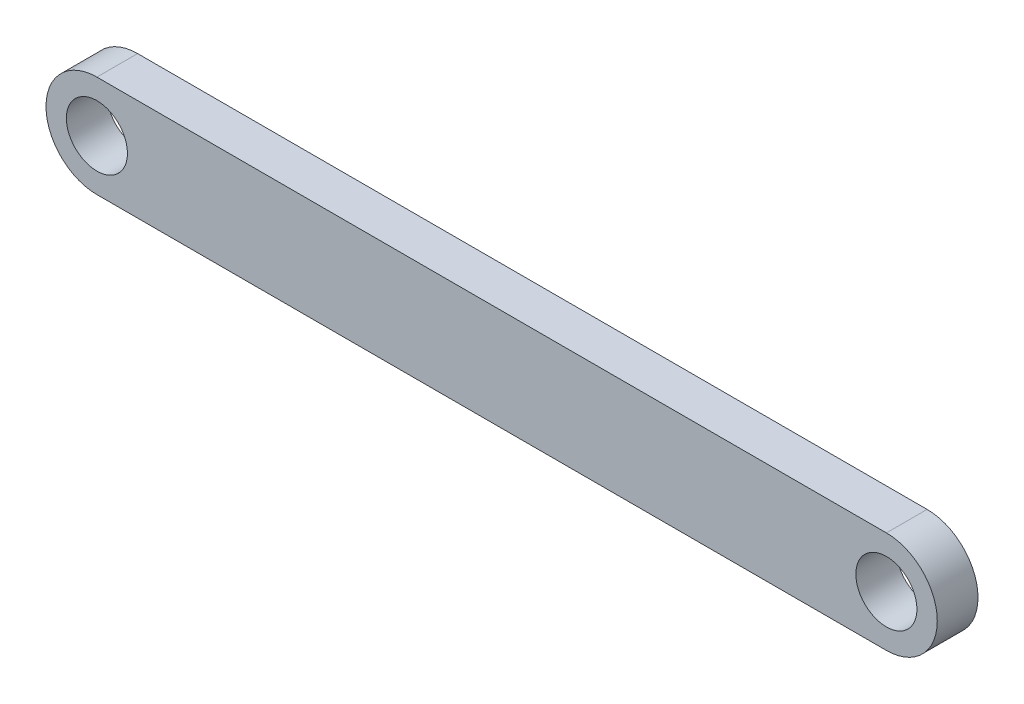
SolidWorks part; units mm, degrees
ref_plane "Front Plane" through (0, 0, 0) normal (0, 0, 1) x (1, 0, 0)
ref_plane "Top Plane" through (0, 0, 0) normal (0, 1, 0) x (1, 0, 0)
ref_plane "Right Plane" through (0, 0, 0) normal (1, 0, 0) x (0, 0, -1)
sketch "Sketch1" plane through (0, 0, 0) normal (0, 0, 1) x (1, 0, 0)
  line L0 (0.0871, 0.0023) -> (38.8671, 0.0023) construction
  line L1 (0.0871, 2.5023) -> (38.8671, 2.5023)
  line L2 (0.0871, -2.4977) -> (38.8671, -2.4977)
  arc A0 (0.0871, 2.5023) -> (0.0871, -2.4977) centre (0.0871, 0.0023) ccw
  arc A1 (38.8671, -2.4977) -> (38.8671, 2.5023) centre (38.8671, 0.0023) ccw
  circle A2 centre (0.0871, 0.0023) radius 1.5
  circle A3 centre (38.8671, 0.0023) radius 1.5
  point P2 (19.4771, 0.0023)
  dimension "D2" = 3
  dimension "D3" = 3
  dimension "D1" = 38.78
  dimension "D4" = 5
extrude "Boss-Extrude1" add sketch "Sketch1" along normal blind 2
